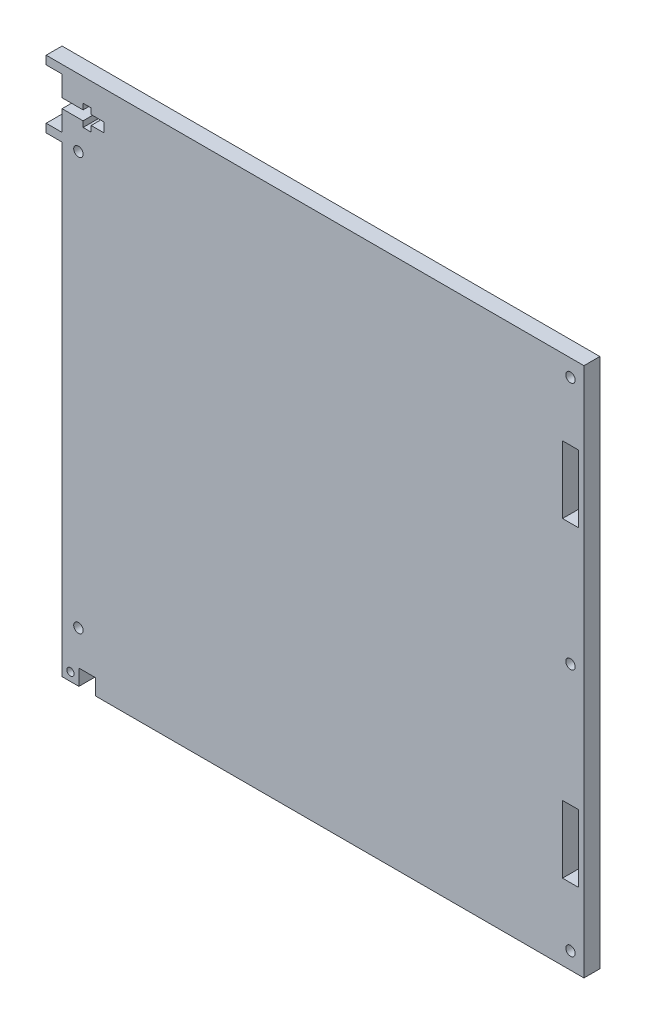
SolidWorks part; units mm, degrees
ref_plane "Front Plane" through (0, 0, 0) normal (0, 0, 1) x (1, 0, 0)
ref_plane "Top Plane" through (0, 0, 0) normal (0, 1, 0) x (1, 0, 0)
ref_plane "Right Plane" through (0, 0, 0) normal (1, 0, 0) x (0, 0, -1)
sketch "Sketch1" plane through (0, 0, 0) normal (0, 0, 1) x (1, 0, 0)
  line L1 (0, 0) -> (196.85, 0)
  line L2 (0, 0) -> (0, 200.025)
  line L3 (0, 200.025) -> (196.85, 200.025)
  line L4 (196.85, 0) -> (196.85, 200.025)
  dimension "D1" = 196.85
  dimension "D2" = 200.025
extrude "Boss-Extrude1" add sketch "Sketch1" against normal blind 5.9944
sketch "Sketch2" plane through (0, 0, 0) normal (0, 0, 1) x (1, 0, 0)
  line L0 (191.77, 200.025) -> (191.77, 0) construction
  line L1 (196.85, 200.025) -> (0, 200.025) construction
  line L2 (0, 0) -> (196.85, 0) construction
  line L3 (196.85, 0) -> (196.85, 200.025) construction
  line L4 (191.77, 171.45) -> (191.77, 146.05) construction
  line L5 (194.7672, 171.45) -> (194.7672, 146.05)
  line L6 (188.7728, 171.45) -> (188.7728, 146.05)
  line L7 (196.85, 100.0125) -> (0, 100.0125) construction
  line L8 (0, 200.025) -> (0, 0) construction
  line L9 (188.7728, 28.575) -> (194.7672, 28.575)
  line L12 (98.425, 200.025) -> (98.425, 0) construction
  line L13 (0, 174.625) -> (98.425, 174.625) construction
  line L16 (0, 187.325) -> (15.875, 187.325) construction
  line L19 (7.9248, 189.103) -> (7.9248, 191.2874)
  line L20 (6.35, 0) -> (12.7, 0)
  line L21 (6.35, 0) -> (6.35, 5.9944)
  line L22 (6.35, 5.9944) -> (12.7, 5.9944)
  line L23 (12.7, 0) -> (12.7, 5.9944)
  line L24 (0, 189.103) -> (7.9248, 189.103)
  line L25 (0, 185.547) -> (7.9248, 185.547)
  line L30 (0, 189.103) -> (0, 185.547)
  line L31 (10.9728, 189.103) -> (15.875, 189.103)
  line L32 (15.875, 189.103) -> (15.875, 185.547)
  line L35 (3.175, 0) -> (3.175, 200.025) construction
  line L36 (10.9728, 185.547) -> (15.875, 185.547)
  line L37 (6.1722, 200.025) -> (6.1722, 0) construction
  line L38 (188.7728, 171.45) -> (194.7672, 171.45)
  line L39 (194.7672, 146.05) -> (188.7728, 146.05)
  line L46 (7.9248, 191.2874) -> (10.9728, 191.2874)
  line L47 (10.9728, 191.2874) -> (10.9728, 189.103)
  line L48 (10.9728, 183.3626) -> (10.9728, 185.547)
  line L49 (7.9248, 183.3626) -> (10.9728, 183.3626)
  line L50 (7.9248, 185.547) -> (7.9248, 183.3626)
  line L51 (194.7672, 28.575) -> (194.7672, 53.975)
  line L52 (194.7672, 53.975) -> (188.7728, 53.975)
  line L53 (188.7728, 28.575) -> (188.7728, 53.975)
  circle A8 centre (191.77, 193.675) radius 1.778
  circle A9 centre (191.77, 100.0125) radius 1.778
  circle A10 centre (191.77, 6.35) radius 1.778
  circle A15 centre (3.175, 3.175) radius 1.3526
  circle A16 centre (6.1722, 174.625) radius 1.778
  circle A17 centre (6.1722, 19.05) radius 1.778
  point P10 (191.77, 146.05)
  dimension "D2" = 25.4
  dimension "D5" = 3.556
  dimension "D6" = 3.556
  dimension "D7" = 6.35
  dimension "D8" = 2.7051
  dimension "D13" = 25.4
  dimension "D14" = 7.9248
  dimension "D26" = 3.556
  dimension "D27" = 3.556
  dimension "D1" = 5.08
  dimension "D3" = 28.575
  dimension "D4" = 25.4
  dimension "D9" = 3.175
  dimension "D10" = 5.9944
  dimension "D11" = 6.35
  dimension "D12" = 6.35
  dimension "D15" = 12.7
  dimension "D16" = 1.778
  dimension "D17" = 3.9624
  dimension "D18" = 3.048
  dimension "D20" = 15.875
  dimension "D21" = 5.9944
  dimension "D24" = 3.175
  dimension "D25" = 2.9972
  dimension "D28" = 19.05
  dimension "D29" = 25.4
  dimension "D30" = 3.175
extrude "Cut-Extrude1" cut sketch "Sketch2" against normal through all
sketch "Sketch3" plane through (0, 0, 0) normal (0, 0, 1) x (1, 0, 0)
  line L0 (15.875, 187.325) -> (-8.7283, 187.325) construction
  line L1 (0, 200.025) -> (-5.9944, 200.025)
  line L2 (0, 200.025) -> (0, 196.85)
  line L3 (0, 196.85) -> (-5.9944, 196.85)
  line L4 (-5.9944, 200.025) -> (-5.9944, 196.85)
  line L5 (15.875, 185.547) -> (15.875, 189.103) construction
  line L6 (0, 177.8) -> (-5.9944, 177.8)
  line L7 (-5.9944, 174.625) -> (-5.9944, 177.8)
  line L8 (0, 174.625) -> (-5.9944, 174.625)
  line L9 (0, 174.625) -> (0, 177.8)
  dimension "D1" = 5.9944
  dimension "D2" = 3.175
extrude "Boss-Extrude2" add sketch "Sketch3" against normal up to surface (5.9944 mm away) up to face at (193.548, 193.675, -5.9944)
